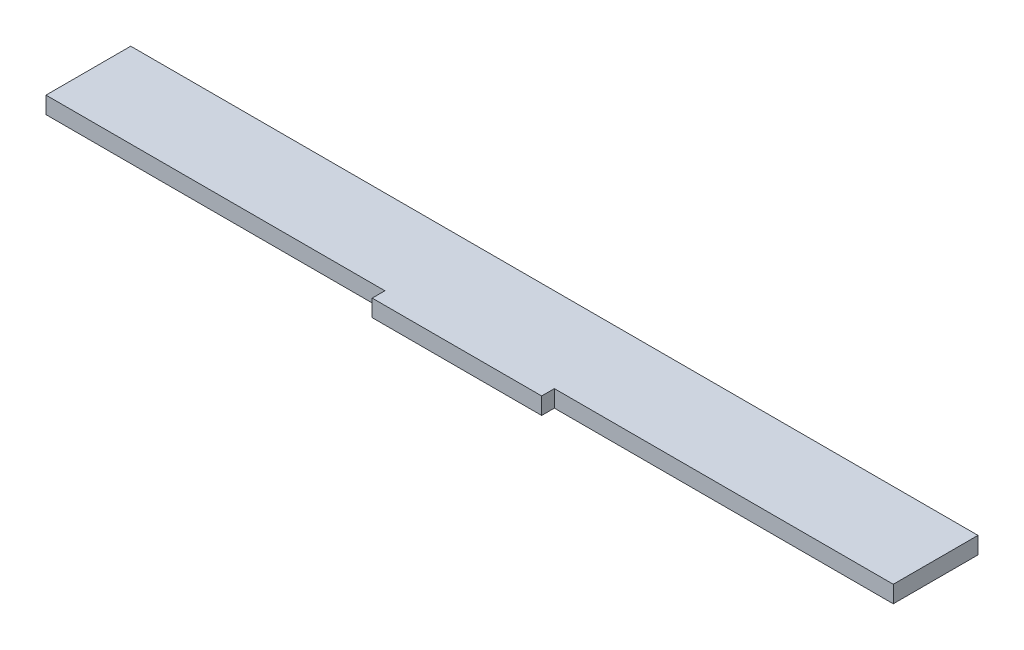
SolidWorks part; units mm, degrees
ref_plane "Přední rovina" through (0, 0, 0) normal (0, 0, 1) x (1, 0, 0)
ref_plane "Horní rovina" through (0, 0, 0) normal (0, 1, 0) x (1, 0, 0)
ref_plane "Pravá rovina" through (0, 0, 0) normal (1, 0, 0) x (0, 0, -1)
sketch "Sketch1" plane through (0, 0, 0) normal (0, 1, 0) x (1, 0, 0)
  line L0 (0, 10) -> (0, -78.618) construction
  line L1 (-100, -10) -> (100, -10)
  line L2 (-100, -10) -> (-100, 10)
  line L3 (-100, 10) -> (100, 10)
  line L4 (100, -10) -> (100, 10)
  line L5 (-100, -10) -> (100, 10) construction
  line L6 (-100, 10) -> (100, -10) construction
  line L7 (-20, -10) -> (20, -10)
  line L8 (-20, -10) -> (-20, -13)
  line L9 (-20, -13) -> (20, -13)
  line L10 (20, -10) -> (20, -13)
  point P0 (0, 0)
  dimension "D1" = 200
  dimension "D2" = 20
  dimension "D3" = 3
  dimension "D4" = 40
extrude "Extrude1" add sketch "Sketch1" along normal blind 4 contours L1 L4 L3 L2 | L9 L10 L7 L8
